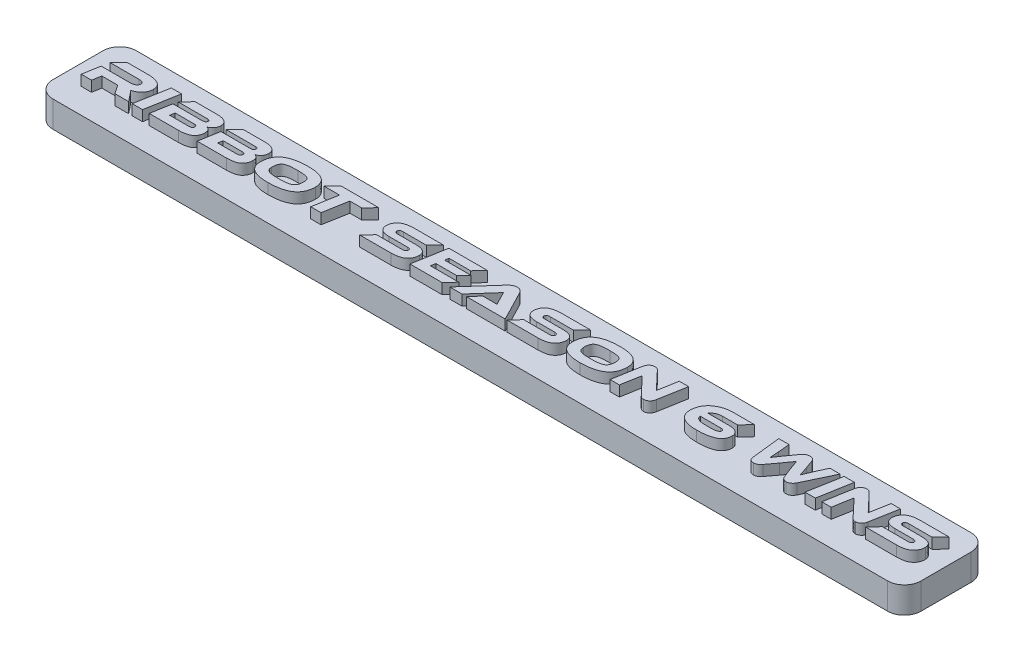
SolidWorks part; units mm, degrees
ref_plane "Front Plane" through (0, 0, 0) normal (0, 0, 1) x (1, 0, 0)
ref_plane "Top Plane" through (0, 0, 0) normal (0, 1, 0) x (1, 0, 0)
ref_plane "Right Plane" through (0, 0, 0) normal (1, 0, 0) x (0, 0, -1)
sketch "Sketch1" plane through (0, 0, 0) normal (0, 1, 0) x (1, 0, 0)
  line L0 (-82.55, -3.175) -> (82.55, -3.175) construction
  line L1 (-82.55, -7.9375) -> (82.55, -7.9375)
  line L2 (-82.55, -7.9375) -> (-82.55, 7.9375)
  line L3 (-82.55, 7.9375) -> (82.55, 7.9375)
  line L4 (82.55, -7.9375) -> (82.55, 7.9375)
  line L5 (-82.55, -7.9375) -> (82.55, 7.9375) construction
  line L6 (-82.55, 7.9375) -> (82.55, -7.9375) construction
  point P0 (0, 0)
  dimension "D1" = 165.1
  dimension "D2" = 15.875
  dimension "D3" = 4.7625
extrude "Boss-Extrude1" add sketch "Sketch1" against normal blind 5
fillet "Fillet1" radius 3.175 4 edges at (82.55, -2.5, -7.9375) (-82.55, -2.5, 7.9375) (82.55, -2.5, 7.9375) (-82.55, -2.5, -7.9375)
sketch "Sketch2" plane through (0, 0, 0) normal (0, 1, 0) x (1, 0, 0)
  line L0 (-82.55, -3.175) -> (82.55, -3.175) construction
  line L1 (82.55, -4.7625) -> (82.55, 4.7625) construction
  line L2 (-82.55, 4.7625) -> (-82.55, -4.7625) construction
  text T0 "Ribbot Season 6 Wins" font "Ethnocentric Rg" height in points 24
  dimension "D1" = 3.175
extrude "Boss-Extrude2" add sketch "Sketch2" along normal blind 2
sketch "Sketch3" plane through (0, -5, 0) normal (0, -1, 0) x (1, 0, 0)
  line L0 (-77.7875, 0) -> (0, 0) construction
  line L1 (0, 0) -> (77.7875, 0) construction
  line L2 (-82.55, -4.7625) -> (-82.55, 4.7625) construction
  circle A0 centre (-77.7875, 0) radius 0.9
  circle A1 centre (0, 0) radius 0.9
  circle A2 centre (77.7875, 0) radius 0.9
  dimension "D2" = 1.8
  dimension "D1" = 4.7625
extrude "Cut-Extrude1" cut sketch "Sketch3" against normal blind 4
